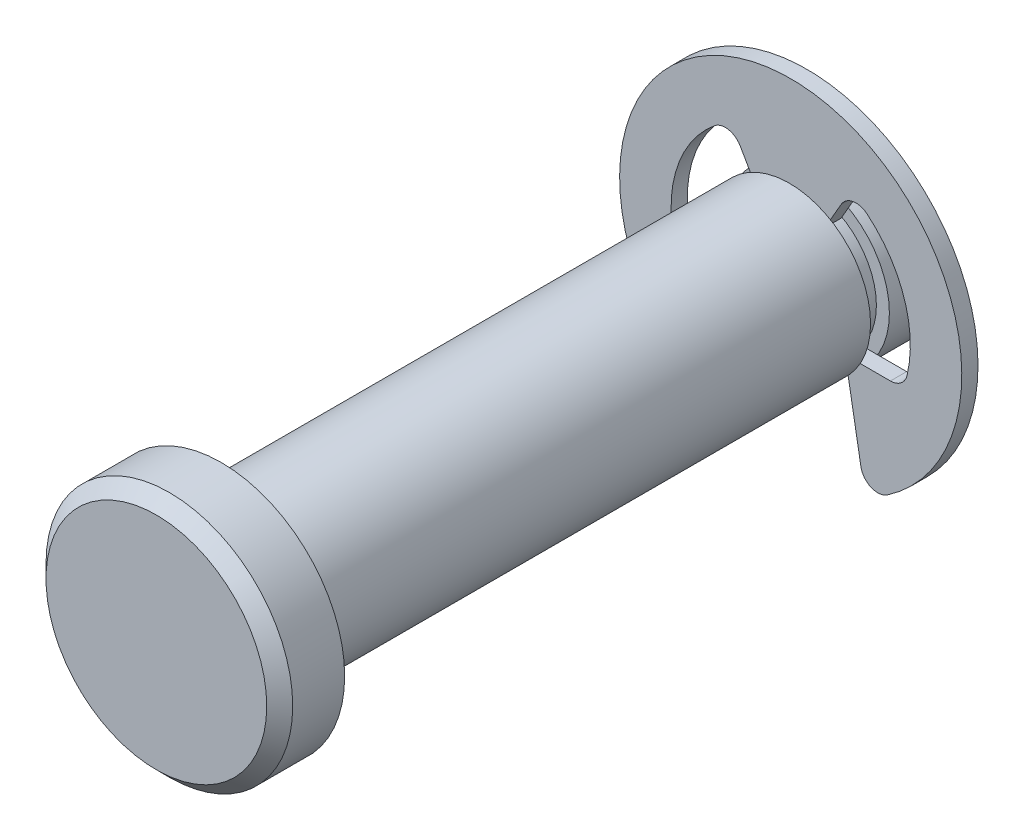
SolidWorks part; units mm, degrees
ref_plane "Front" through (0, 0, 0) normal (0, 0, 1) x (1, 0, 0)
ref_plane "Top" through (0, 0, 0) normal (0, 1, 0) x (1, 0, 0)
ref_plane "Right" through (0, 0, 0) normal (1, 0, 0) x (0, 0, -1)
sketch "Sketch2" plane through (0, 0, 0) normal (0, 0, 1) x (1, 0, 0)
  circle A0 centre (0, 0) radius 3.175
  point P3 (0, 3.175)
  point P4 (0, -3.175)
  dimension "dia" = 6.35
extrude "Extrude1" add sketch "Sketch2" along normal mid plane 25.4
sketch "Sketch3" plane through (0, 0, 0) normal (1, 0, 0) x (0, 0, -1)
  line L0 (12.7, 3.175) -> (-12.7, 3.175) construction
  line L1 (9.525, 3.175) -> (10.2616, 3.175)
  line L2 (9.525, 3.175) -> (9.525, 2.667)
  line L3 (9.525, 2.667) -> (10.2616, 2.667)
  line L4 (10.2616, 3.175) -> (10.2616, 2.667)
  line L5 (-12.7, 3.175) -> (-12.7, -3.175) construction
  line L10 (10.2616, 2.667) -> (10.2616, -2.667) construction
  point P11 (10.2616, 0)
  point P14 (9.8933, 3.175)
  dimension "groove wd" = 0.7366
  dimension "groove dia" = 5.334
  dimension "usable lg" = 22.225
revolve "Cut-Revolve1" cut sketch "Sketch3" angle 360 about axis through (0, 0, 12.7) along (0, 0, -1)
sketch "Sketch8" plane through (0, 0, 12.7) normal (0, 0, 1) x (1, 0, 0)
  circle A0 centre (0, 0) radius 4.826
  dimension "head dia" = 9.652
extrude "Extrude6" add sketch "Sketch8" along normal blind 2.54
chamfer "Chamfer2" distance 0.508 angle 45 1 edges at (4.826, 0, 15.24)
ref_plane "Plane1" through (0, 0, -9.8933) normal (0, 0, 1) x (1, 0, 0)
sketch "Sketch4" plane through (0, 0, -9.8933) normal (0, 0, 1) x (1, 0, 0)
  line L0 (0, 2.667) -> (0, -2.667) construction
  circle A0 centre (0, 0) radius 6.6929
  circle A1 centre (0, 0) radius 2.667
  dimension "ring dia" = 13.3858
extrude "Extrude2" add sketch "Sketch4" along normal mid plane 0.635 separate body
sketch "Sketch5" plane through (0, 0, 0) normal (0, 0, 1) x (1, 0, 0)
  line L0 (0, 6.6929) -> (0, 2.667) construction
  line L1 (-2.34, 4.053) -> (0, 0)
  line L2 (-4.3979, -1.6002) -> (-2.1336, -1.6002)
  line L3 (0, 0) -> (2.34, 4.053)
  line L4 (-2.1336, -1.6002) -> (-2.9139, -6.0253)
  line L5 (2.1336, -1.6002) -> (2.9139, -6.0253)
  line L6 (2.1336, -1.6002) -> (4.3979, -1.6002)
  arc A0 (-2.34, 4.053) -> (-4.3979, -1.6002) centre (0, 0) ccw
  circle A1 centre (0, 0) radius 6.6929 construction
  circle A2 centre (0, 0) radius 2.667 construction
  arc A3 (4.3979, -1.6002) -> (2.34, 4.053) centre (0, 0) ccw
  arc A4 (-2.9139, -6.0253) -> (2.9139, -6.0253) centre (0, 0) ccw
  circle A5 centre (0, 0) radius 2.667 construction
  point P10 (0, 4.6799)
  dimension "D1" = 30
  dimension "D2" = 10
  dimension "D3" = 1.6002
extrude "Extrude4" cut sketch "Sketch5" against normal through all
sketch "Sketch6" plane through (0, 0, -9.5758) normal (0, 0, 1) x (1, 0, 0)
  line L0 (-1.3335, 2.3097) -> (1.3335, 2.3097)
  circle A0 centre (0, 0) radius 2.667 construction
  arc A1 (1.3335, 2.3097) -> (-1.3335, 2.3097) centre (0, 0) ccw
extrude "Extrude5" add sketch "Sketch6" against normal up to surface (0.635 mm away) up to face at (0, 0.8098, -10.2108)
fillet "Fillet1" radius 0.6693 6 edges at (2.9139, -6.0253, -9.8933) (-2.9139, -6.0253, -9.8933) (4.3979, -1.6002, -9.8933) (2.34, 4.053, -9.8933) (-2.34, 4.053, -9.8933) (-4.3979, -1.6002, -9.8933)
chamfer "Chamfer1" distance 0.635 angle 45 1 edges at (3.175, 0, -12.7)
sketch "Sketch7" plane through (0, 0, 0) normal (1, 0, 0) x (0, 0, -1)
  line L0 (10.2108, 6.6929) -> (9.5758, 6.6929) construction
  line L1 (12.7, -3.175) -> (12.7, 3.175) construction
  line L2 (9.5758, -5.6368) -> (10.2108, -5.6368) construction
  line L3 (-15.24, 4.318) -> (-15.24, -4.318) construction
  point P0 (10.2616, -5.6368)
  point P1 (12.7, 3.175)
  point P2 (-15.24, 4.826)
  point P6 (9.525, 6.6929)
  point P7 (12.7, -3.175)
  point P12 (-12.7, 4.826)
  point P16 (9.525, -5.6368)
equation "\"D1@Chamfer1\" = \"dia@Sketch2\" * .1"
equation "\"D1@Fillet1\" = \"ring dia@Sketch4\" * .05"
equation "\"D3@Sketch5\" = \"groove dia@Sketch3\" * .3"
equation "\"D1@Chamfer2\" = \"head ht@Extrude6\" * .2"
